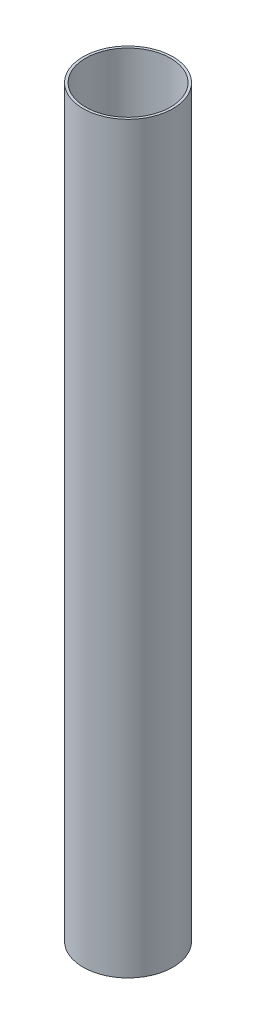
SolidWorks part; units mm, degrees
ref_plane "Front Plane" through (0, 0, 0) normal (0, 0, 1) x (1, 0, 0)
ref_plane "Top Plane" through (0, 0, 0) normal (0, 1, 0) x (1, 0, 0)
ref_plane "Right Plane" through (0, 0, 0) normal (1, 0, 0) x (0, 0, -1)
sketch "Sketch1" plane through (0, 0, 0) normal (0, 0, 1) x (1, 0, 0)
  line L0 (0, 0) -> (0, 304.8) construction
  line L1 (-15.35, 0) -> (-14.5, 0)
  line L2 (-15.35, 0) -> (-15.35, 254)
  line L3 (-15.35, 254) -> (-14.5, 254)
  line L4 (15.35, 0) -> (15.35, 254)
  line L5 (-14.5, 0) -> (-14.5, 254)
  line L6 (14.5, 254) -> (14.5, 0)
  line L7 (14.5, 0) -> (15.35, 0)
  line L8 (14.5, 254) -> (15.35, 254)
  dimension "D1" = 30.7
  dimension "12" = 254
  dimension "D2" = 29
revolve "Revolve2" add sketch "Sketch1" angle 360 about L0
